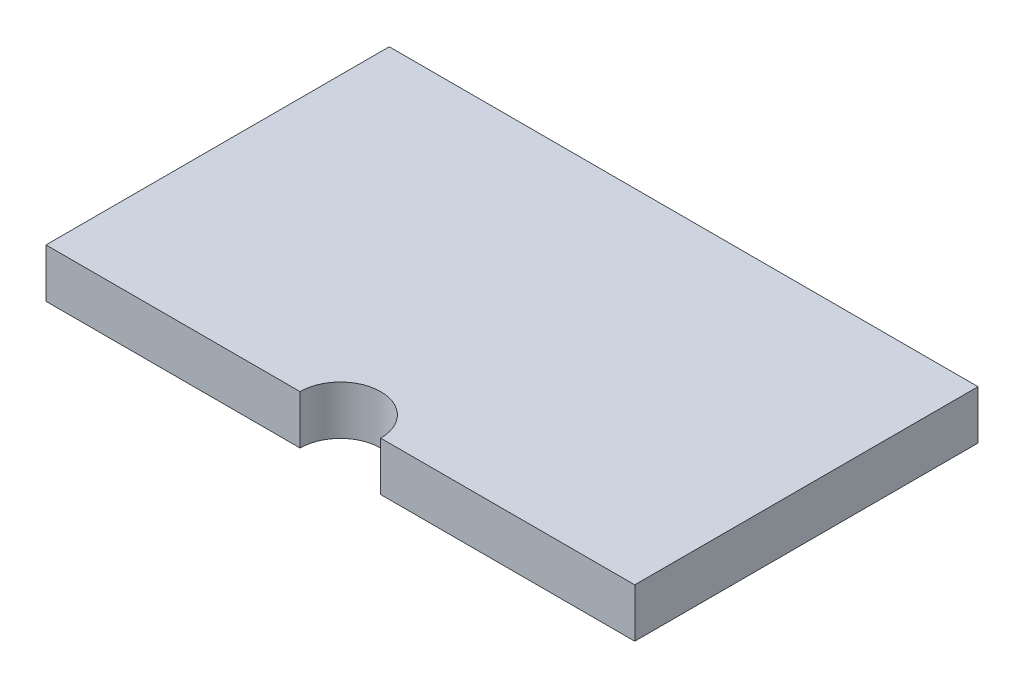
SolidWorks part; units mm, degrees
ref_plane "Front Plane" through (0, 0, 0) normal (0, 0, 1) x (1, 0, 0)
ref_plane "Top Plane" through (0, 0, 0) normal (0, 1, 0) x (1, 0, 0)
ref_plane "Right Plane" through (0, 0, 0) normal (1, 0, 0) x (0, 0, -1)
sketch "Sketch1" plane through (0, 0, 0) normal (0, 1, 0) x (1, 0, 0)
  line L1 (-30.607, 17.8435) -> (30.607, 17.8435)
  line L2 (-30.607, 17.8435) -> (-30.607, -17.8435)
  line L3 (-30.607, -17.8435) -> (30.607, -17.8435)
  line L4 (30.607, 17.8435) -> (30.607, -17.8435)
  line L5 (-30.607, 17.8435) -> (30.607, -17.8435) construction
  line L6 (-30.607, -17.8435) -> (30.607, 17.8435) construction
  point P0 (0, 0)
  dimension "D1" = 35.687
  dimension "D2" = 61.214
extrude "Boss-Extrude1" add sketch "Sketch1" along normal blind 5.08
sketch "Sketch2" plane through (0, 5.08, 0) normal (0, 1, 0) x (1, 0, 0)
  line L0 (-30.607, -17.8435) -> (30.607, -17.8435) construction
  circle A0 centre (0, -17.8435) radius 4.191
  dimension "D1" = 8.382
extrude "Cut-Extrude1" cut sketch "Sketch2" against normal through all
